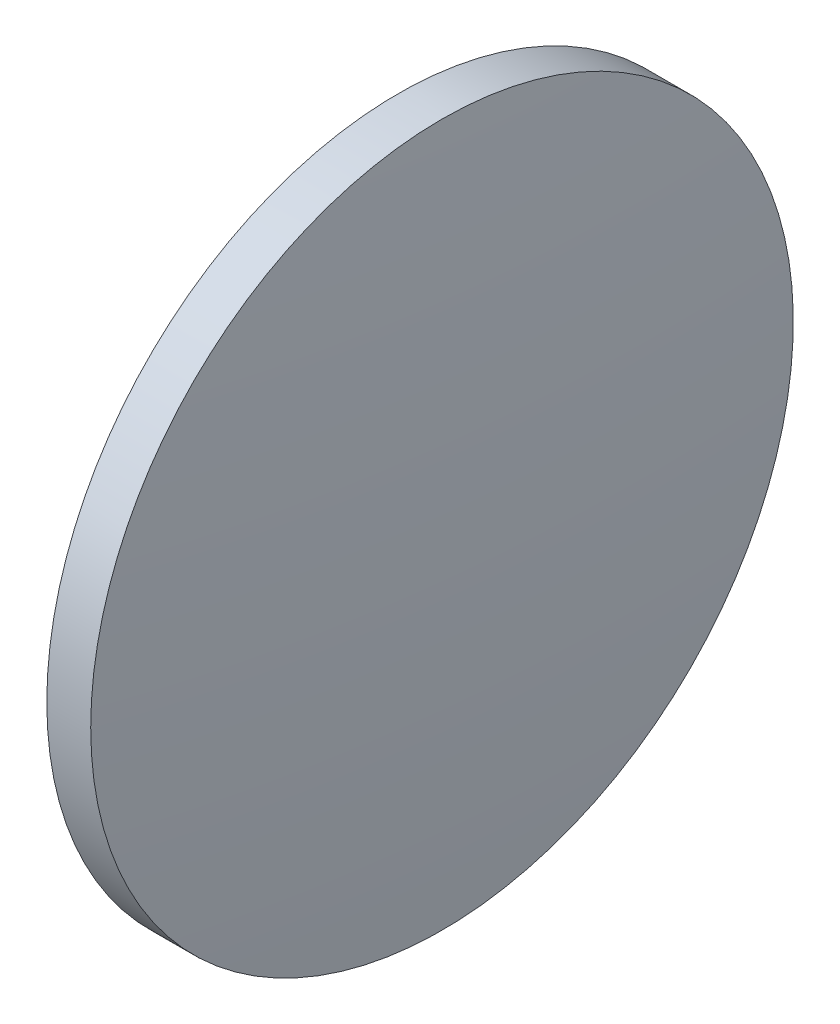
SolidWorks part; units mm, degrees
ref_plane "前视基准面" through (0, 0, 0) normal (0, 0, 1) x (1, 0, 0)
ref_plane "上视基准面" through (0, 0, 0) normal (0, 1, 0) x (1, 0, 0)
ref_plane "右视基准面" through (0, 0, 0) normal (1, 0, 0) x (0, 0, -1)
sketch "草图2" plane through (0, 0, 0) normal (0, 0, 1) x (1, 0, 0)
  line L0 (1328.2397, 411.5874) -> (1347.4159, 411.5874) construction
  line L1 (1332.9343, 411.5874) -> (1332.9343, 431.5874)
  line L2 (1336.2143, 411.5874) -> (1332.9343, 411.5874)
  line L5 (1332.9343, 431.5874) -> (1335.4343, 431.5874)
  arc A0 (1336.2143, 411.5874) -> (1335.4343, 431.5874) centre (1079.414, 411.5874) ccw
revolve "旋转2" add sketch "草图2" angle 360 about L0
